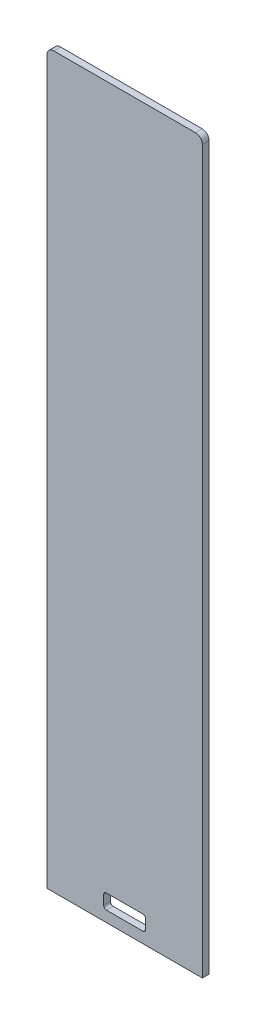
SolidWorks part; units mm, degrees
ref_plane "Front Plane" through (0, 0, 0) normal (0, 0, 1) x (1, 0, 0)
ref_plane "Top Plane" through (0, 0, 0) normal (0, 1, 0) x (1, 0, 0)
ref_plane "Right Plane" through (0, 0, 0) normal (1, 0, 0) x (0, 0, -1)
sketch "Sketch1" plane through (0, 0, 0) normal (0, 0, 1) x (1, 0, 0)
  line L0 (0, 0) -> (0, 607.3559) construction
  line L1 (-57.5, 499.2) -> (57.5, 499.2)
  line L2 (-57.5, 499.2) -> (-57.5, 0)
  line L3 (-57.5, 0) -> (57.5, 0)
  line L4 (57.5, 499.2) -> (57.5, 0)
  dimension "D1" = 499.2
  dimension "D2" = 115
extrude "Boss-Extrude1" add sketch "Sketch1" along normal blind 5
sketch "Sketch2" plane through (0, 0, 5) normal (0, 0, 1) x (1, 0, 0)
  line L0 (0, 0) -> (0, 190.7032) construction
  line L1 (-15.5, 19) -> (15.5, 19)
  line L2 (-15.5, 19) -> (-15.5, 8)
  line L3 (-15.5, 8) -> (15.5, 8)
  line L4 (15.5, 19) -> (15.5, 8)
  line L5 (-57.5, 0) -> (57.5, 0) construction
  dimension "D1" = 31
  dimension "D2" = 11
  dimension "D3" = 8
extrude "Cut-Extrude1" cut sketch "Sketch2" against normal up to next
fillet "Fillet1" radius 2 4 edges at (15.5, 8, 2.5) (15.5, 19, 2.5) (-15.5, 8, 2.5) (-15.5, 19, 2.5)
sketch "Sketch3" plane through (0, 0, 5) normal (0, 0, 1) x (1, 0, 0)
  line L0 (57.5, 0) -> (57.5, 499.2) construction
  line L1 (-57.5, 539.2) -> (57.5, 539.2)
  line L2 (-57.5, 539.2) -> (-57.5, 499.2)
  line L3 (-57.5, 499.2) -> (57.5, 499.2)
  line L4 (57.5, 539.2) -> (57.5, 499.2)
  line L5 (-57.5, 499.2) -> (-57.5, 0) construction
  line L6 (57.5, 499.2) -> (-57.5, 499.2) construction
  dimension "D1" = 40
extrude "Boss-Extrude2" add sketch "Sketch3" against normal blind 5
fillet "Fillet2" radius 5 2 edges at (-57.5, 539.2, 2.5) (57.5, 539.2, 2.5)
